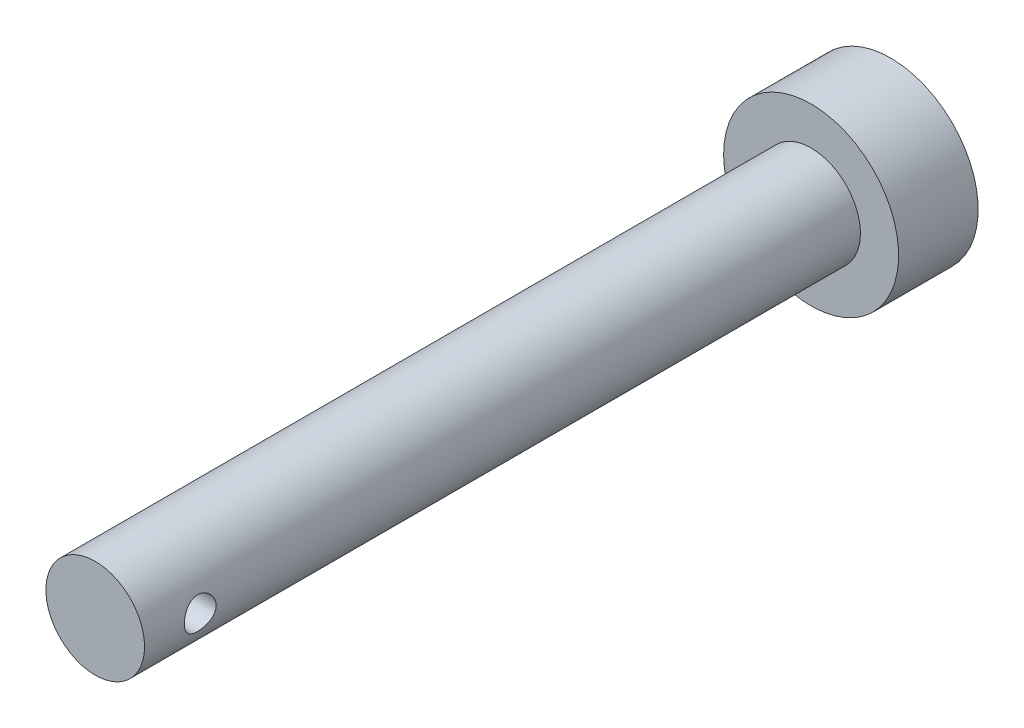
SolidWorks part; units mm, degrees
ref_plane "Front Plane" through (0, 0, 0) normal (0, 0, 1) x (1, 0, 0)
ref_plane "Top Plane" through (0, 0, 0) normal (0, 1, 0) x (1, 0, 0)
ref_plane "Right Plane" through (0, 0, 0) normal (1, 0, 0) x (0, 0, -1)
sketch "Sketch1" plane through (0, 0, 0) normal (0, 0, 1) x (1, 0, 0)
  circle A0 centre (0, 0) radius 3.1
  dimension "D1" = 6.2
extrude "Boss-Extrude1" add sketch "Sketch1" along normal blind 45
sketch "Sketch2" plane through (0, 0, 0) normal (1, 0, 0) x (0, 0, -1)
  line L0 (3.41, 0) -> (-3.41, 0) construction
  line L1 (-45, 3.1) -> (-45, -3.1) construction
  circle A0 centre (-41.5, 0) radius 1
  point P4 (-40.1257, 0)
  point P5 (-41.0401, 0)
  dimension "D1" = 2
  dimension "D2" = 3.5
extrude "Cut-Extrude1" cut sketch "Sketch2" against normal through all both and the other way through all
sketch "Sketch3" plane through (0, 0, 0) normal (0, 0, -1) x (-1, 0, 0)
  circle A0 centre (0, 0) radius 5.5
  dimension "D1" = 11
extrude "Boss-Extrude2" add sketch "Sketch3" along normal blind 5
